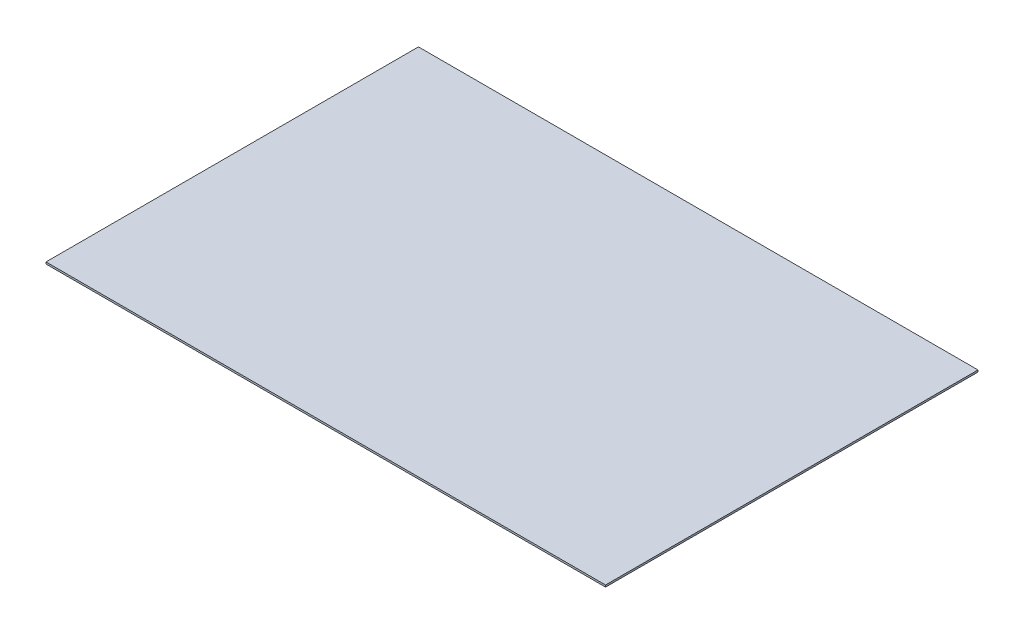
SolidWorks part; units mm, degrees
ref_plane "Front Plane" through (0, 0, 0) normal (0, 0, 1) x (1, 0, 0)
ref_plane "Top Plane" through (0, 0, 0) normal (0, 1, 0) x (1, 0, 0)
ref_plane "Right Plane" through (0, 0, 0) normal (1, 0, 0) x (0, 0, -1)
sketch "Sketch1" plane through (0, 0, 0) normal (0, 1, 0) x (1, 0, 0)
  line L1 (0, 0) -> (600, 0)
  line L2 (0, 0) -> (0, 399.38)
  line L3 (0, 399.38) -> (600, 399.38)
  line L4 (600, 0) -> (600, 399.38)
  dimension "D1" = 399.38
  dimension "D2" = 600
extrude "Boss-Extrude1" add sketch "Sketch1" along normal blind 2
